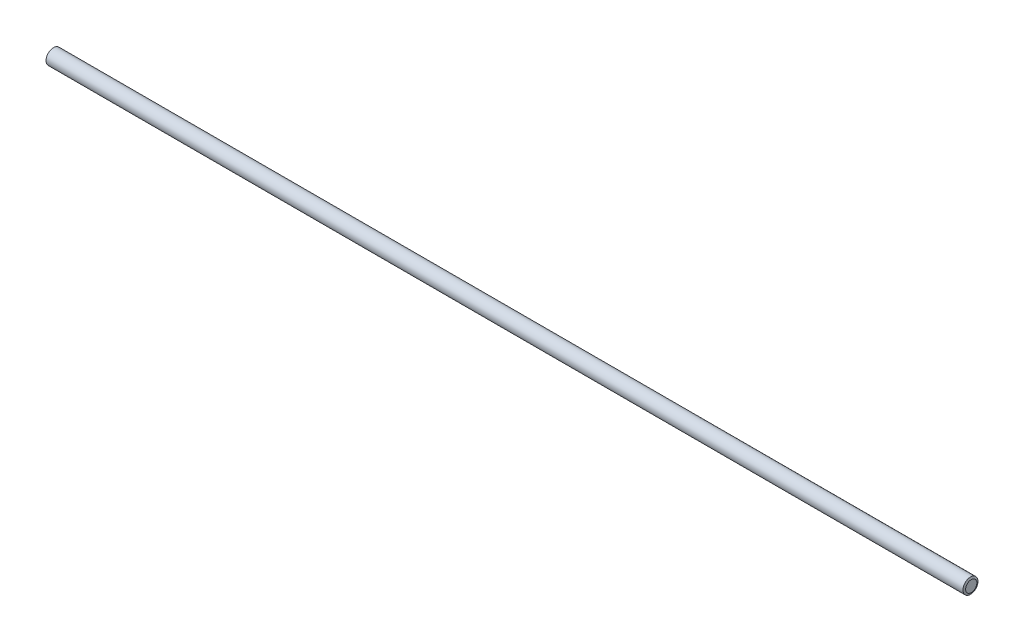
SolidWorks part; units mm, degrees
material "Alloy Steel"
ref_plane "Front Plane" through (0, 0, 0) normal (0, 0, 1) x (1, 0, 0)
ref_plane "Top Plane" through (0, 0, 0) normal (0, 1, 0) x (1, 0, 0)
ref_plane "Right Plane" through (0, 0, 0) normal (1, 0, 0) x (0, 0, -1)
ref_plane "Plane1" through (0, 0, 0) normal (0, 0, 1) x (1, 0, 0)
sketch "Sketch1" plane through (0, 0, 0) normal (0, 0, 1) x (1, 0, 0)
  line L0 (0, 0) -> (0, 3.7369)
  line L1 (0, 3.7369) -> (0.5, 5)
  line L2 (0.5, 5) -> (609.5, 5)
  line L3 (609.5, 5) -> (610, 3.7369)
  line L4 (610, 3.7369) -> (610, 0)
  line L5 (610, 0) -> (0, 0)
  line L6 (610, 0) -> (0, 0) construction
  line L7 (305, 0) -> (305, 5) construction
  dimension "D1" = 610
  dimension "D2" = 21.597
  dimension "D3" = 5
  dimension "D4" = 1.2631
  dimension "D5" = 21.597
revolve "Revolve1" add sketch "Sketch1" angle 360 about L6
